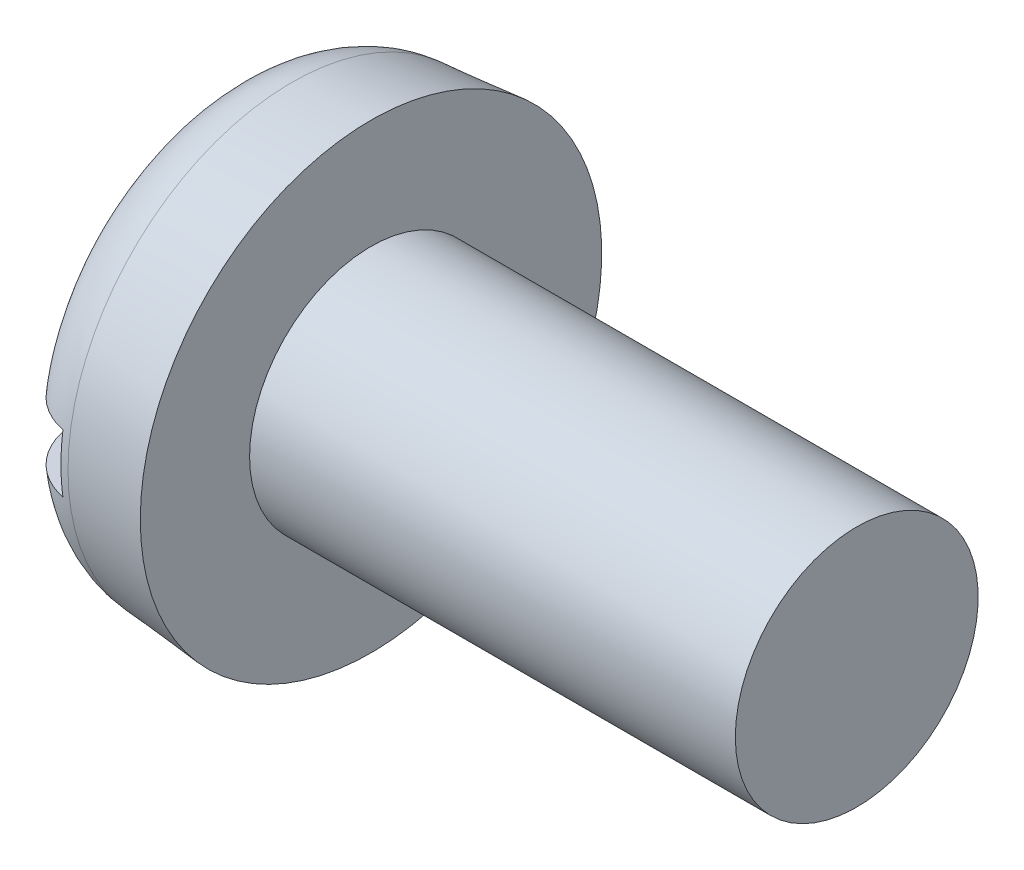
SolidWorks part; units mm, degrees
ref_plane "Plane1" through (0, 0, 0) normal (0, 0, 1) x (1, 0, 0)
ref_plane "Plane2" through (0, 0, 0) normal (0, 1, 0) x (1, 0, 0)
ref_plane "Plane3" through (0, 0, 0) normal (1, 0, 0) x (0, 0, -1)
sketch "BodySke" plane through (0, 0, 0) normal (0, 0, 1) x (1, 0, 0)
  line L0 (3, 2.5) -> (3, 4.75)
  line L1 (0, 0) -> (0, 4.4875)
  line L2 (-25.4, 0) -> (127, 0) construction
  line L3 (13, 0) -> (0, 0)
  line L4 (3, 2.5) -> (13, 2.5)
  line L5 (13, 2.5) -> (13, 0)
  line L6 (0, 4.4875) -> (3, 4.75)
  line L9 (3.8, 4.0875) -> (3.8, -5.4375) construction
  line L10 (3, 6.35) -> (3, -3.175) construction
  dimension "Head_ht" = 3
  dimension "Diameter" = 5
  dimension "Length" = 10
  dimension "Head_dia" = 9.5
  dimension "Advance" = 0.8
  dimension "Thread_nom" = 10
  dimension "Head_side_angle" = 5
revolve "Base-Revolve" add sketch "BodySke"
cosmetic thread "ThreadCosmetic"
fillet "Fillet1" [suppressed] radius 0.2
fillet "Fillet2" radius 1.5 1 edges at (0, 0, 4.4875)
sketch "Sketch2" plane through (0, 0, 0) normal (1, 0, 0) x (0, 0, -1)
  line L0 (4.75, -0.6) -> (-4.75, -0.6)
  line L1 (4.75, -0.6) -> (4.75, 0.6)
  line L2 (-4.75, 0.6) -> (4.75, 0.6)
  line L3 (-4.75, 0.6) -> (-4.75, -0.6)
  dimension "D1" = 9.5
  dimension "D2" = 4.75
  dimension "Slot_width" = 1.2
  dimension "D3" = 0.6
extrude "Slot" cut sketch "Sketch2" along normal blind 1.2
sketch "ThdSchSke" plane through (0, 0, 0) normal (0, 0, 1) x (1, 0, 0)
  line L0 (4.6, -2.055) -> (4.2884, -2.5)
  line L1 (4.6, -2.055) -> (4.9116, -2.5)
  line L2 (4.9116, -2.5) -> (4.9116, -3.125)
  line L3 (-3.175, 0) -> (5.1513, 0) construction
  line L5 (4.9116, -3.125) -> (4.2884, -3.125)
  line L6 (4.2884, -3.125) -> (4.2884, -2.5)
  dimension "Thread_minor" = 4.11
  dimension "Diameter" = 5
  dimension "Start" = 4.6
  dimension "SideAngle" = 55
  dimension "VeeAngle" = 70
  dimension "Overcut" = 6.25
revolve "ThreadSchematic" [suppressed] cut sketch "ThdSchSke" angle 360 about L3
pattern_linear "ThdSchPat" [suppressed]
equation "\"D1@Sketch2\" = \"Head_dia@BodySke\""
equation "\"D2@Sketch2\" = \"D1@Sketch2\" / 2"
equation "\"D3@Sketch2\" = \"Slot_width@Sketch2\" / 2"
equation "\"Thread_length@ThreadCosmetic\" = ((sgn( (\"Length@BodySke\" - \"Advance@BodySke\" * 2.0 ) - \"Thread_nom@BodySke\" )-1)*( (\"Length@BodySke\" - \"Advance@BodySke\"  * 2.0) - \"Thread_nom@BodySke\" ))/-2+ \"Thread_nom@BodySke\""
equation "\"Thread_minor@ThdSchSke\" = \"Thread_minor@ThreadCosmetic\""
equation "\"Diameter@ThdSchSke\" = \"Diameter@BodySke\""
equation "\"Overcut@ThdSchSke\" = \"Diameter@BodySke\" * 1.25"
equation "\"Start@ThdSchSke\" = \"Head_ht@BodySke\" + \"Length@BodySke\" - \"Thread_length@ThreadCosmetic\"  '---Non-countersunk---"
equation "\"Num_threads@ThdSchPat\" = int( \"Thread_length@ThreadCosmetic\" / \"Advance@BodySke\" + 0.999 )  + 1"
equation "\"Advance@ThdSchPat\" = \"Thread_length@ThreadCosmetic\" /  (\"Num_threads@ThdSchPat\" - 1) 'relax it"
